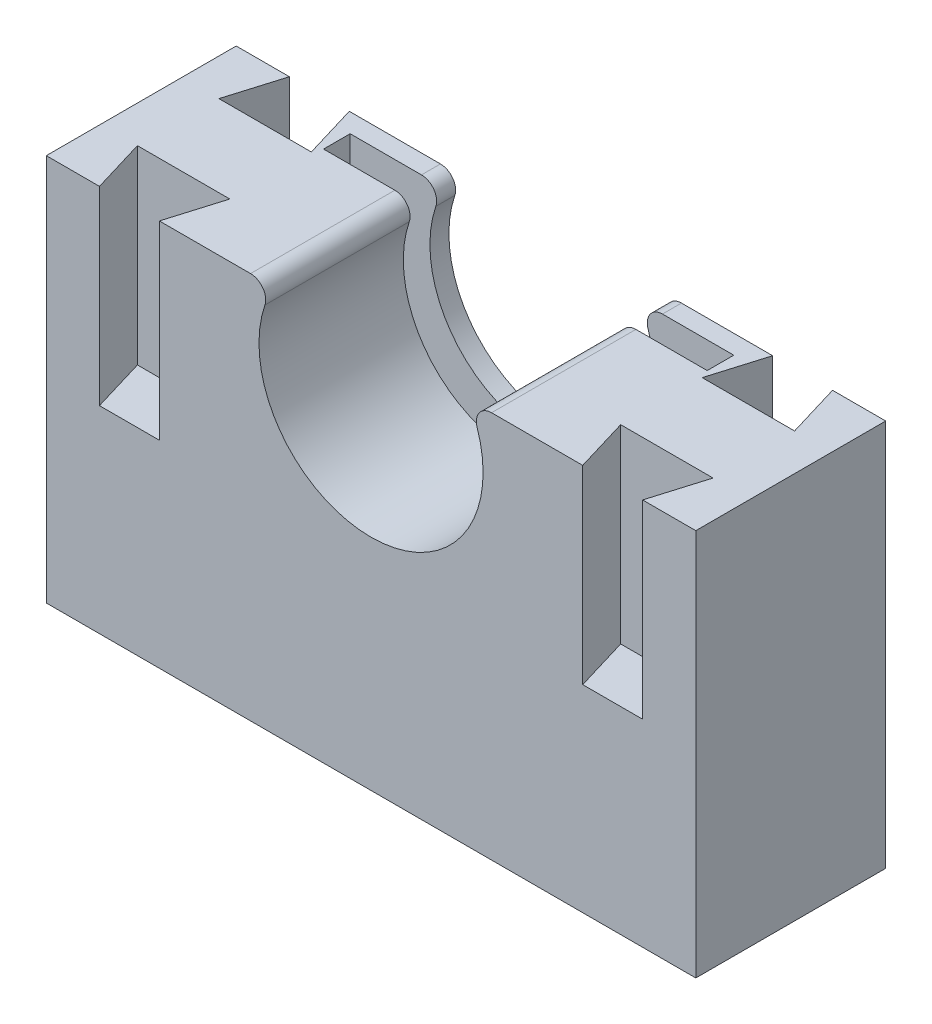
SolidWorks part; units mm, degrees
ref_plane "Front Plane" through (0, 0, 0) normal (0, 0, 1) x (1, 0, 0)
ref_plane "Top Plane" through (0, 0, 0) normal (0, 1, 0) x (1, 0, 0)
ref_plane "Right Plane" through (0, 0, 0) normal (1, 0, 0) x (0, 0, -1)
sketch "Sketch2" plane through (0, 0, 0) normal (0, 0, 1) x (1, 0, 0)
  line L0 (11.1505, 5.8899) -> (11.1505, -22.9851) construction
  line L1 (53.9005, 28.0149) -> (27.0147, 28.0149)
  line L2 (53.9005, 28.0149) -> (53.9005, -22.9851)
  line L3 (53.9005, -22.9851) -> (-31.5995, -22.9851)
  line L4 (-31.5995, 28.0149) -> (-31.5995, -22.9851)
  line L5 (-31.5995, 2.5149) -> (53.9005, 2.5149) construction
  line L6 (-4.7137, 28.0149) -> (-31.5995, 28.0149)
  line L7 (11.1505, 20.6399) -> (11.1505, -22.9851) construction
  line L8 (11.1505, 20.6399) -> (25.1204, 25.3731) construction
  line L9 (-3.5995, 20.6399) -> (25.9005, 20.6399) construction
  arc A0 (-2.8194, 25.3731) -> (25.1204, 25.3731) centre (11.1505, 20.6399) ccw
  arc A1 (-4.7137, 28.0149) -> (-2.8194, 25.3731) centre (-4.7137, 26.0149) cw
  arc A2 (27.0147, 28.0149) -> (25.1204, 25.3731) centre (27.0147, 26.0149) ccw
  dimension "D4" = 2
  dimension "D5" = 29.5
  dimension "D3" = 2
  dimension "D1" = 85.5
  dimension "D2" = 51
extrude "Boss-Extrude1" add sketch "Sketch2" along normal blind 25
sketch "Sketch5" plane through (0, 0, 25) normal (0, 0, 1) x (1, 0, 0)
  line L0 (11.1505, 5.8899) -> (11.1505, 1.4899) construction
  line L1 (-31.5995, -22.9851) -> (53.9005, -22.9851) construction
  line L2 (11.1505, 5.8899) -> (11.1505, 1.4899)
  line L3 (11.1505, -7.3101) -> (11.1505, -22.9851) construction
  arc A0 (-2.8194, 25.3731) -> (25.1204, 25.3731) centre (11.1505, 20.6399) ccw construction
  circle A1 centre (11.1505, -2.9101) radius 4.4
  dimension "D2" = 8.8
  dimension "D1" = 8.8
extrude "Cut-Extrude3" cut sketch "Sketch5" along normal blind 4.5 from surface at -25 contours A1 starting at face at (11.1505, 12.2907, 0)
sketch "Sketch6" plane through (0, 28.0149, 0) normal (0, 1, 0) x (1, 0, 0)
  line L0 (-24.5995, 0) -> (-26.7385, -7.1363)
  line L1 (-4.7137, 0) -> (-31.5995, 0) construction
  line L2 (-26.7385, -7.1363) -> (-14.5747, -7.1363)
  line L3 (-14.5747, -7.1363) -> (-16.7137, 0)
  line L4 (-31.5995, 0) -> (-24.5995, 0)
  line L5 (-16.7137, 0) -> (-4.7137, 0)
  line L6 (-31.5995, -25) -> (-24.5995, -25)
  line L7 (-4.7137, -25) -> (-31.5995, -25) construction
  line L8 (-24.5995, -25) -> (-26.7391, -17.8638)
  line L9 (-26.7391, -17.8638) -> (-14.5741, -17.8638)
  line L10 (-14.5741, -17.8638) -> (-16.7137, -25)
  line L11 (-16.7137, -25) -> (-4.7137, -25)
  line L12 (53.9005, 0) -> (46.9005, 0)
  line L13 (46.9005, 0) -> (49.0401, -7.1362)
  line L14 (49.0401, -7.1362) -> (36.8751, -7.1362)
  line L15 (36.8751, -7.1362) -> (39.0147, 0)
  line L16 (53.9005, 0) -> (27.0147, 0) construction
  line L17 (39.0147, 0) -> (27.0147, 0)
  line L18 (27.0147, -25) -> (39.0147, -25)
  line L19 (53.9005, -25) -> (27.0147, -25) construction
  line L20 (39.0147, -25) -> (36.8751, -17.8638)
  line L21 (36.8751, -17.8638) -> (49.0401, -17.8638)
  line L22 (49.0401, -17.8638) -> (46.9005, -25)
  line L23 (46.9005, -25) -> (53.9005, -25)
  line L24 (-31.5995, 0) -> (-31.5995, -25)
  line L27 (53.9005, 0) -> (53.9005, -25)
  line L28 (-4.7137, 0) -> (27.0147, 0)
  line L29 (27.0147, -25) -> (-4.7137, -25)
  dimension "D1" = 7
  dimension "D2" = 12
  dimension "D3" = 7.45
  dimension "D4" = 7.45
  dimension "D5" = 106.685
  dimension "D6" = 12.1639
  dimension "D7" = 7
  dimension "D8" = 12
  dimension "D9" = 7.45
  dimension "D10" = 7.45
  dimension "D11" = 106.69
  dimension "D12" = 12
  dimension "D13" = 7
  dimension "D14" = 7.45
  dimension "D15" = 7.45
  dimension "D16" = 106.69
  dimension "D17" = 12.165
  dimension "D18" = 12.165
  dimension "D19" = 12
  dimension "D20" = 7
  dimension "D21" = 7.45
  dimension "D22" = 106.69
  dimension "D23" = 7.45
extrude "Cut-Extrude4" cut sketch "Sketch6" against normal blind 25 flip side to cut
ref_plane "Plane1" through (0, 0, 2.5) normal (0, 0, -1) x (-1, 0, 0)
sketch "Sketch8" plane through (0, 0, 2.5) normal (0, 0, -1) x (-1, 0, 0)
  line L0 (-27.0147, 28.0149) -> (4.7137, 28.0149) construction
  line L1 (-11.1505, 28.0149) -> (-11.1505, -7.3101) construction
  line L2 (-36.4005, 2.9448) -> (14.0995, 2.9448)
  line L3 (-36.4005, 2.9448) -> (-36.4005, 28.0149)
  line L4 (-39.0147, 28.0149) -> (-27.0147, 28.0149) construction
  line L5 (-36.4005, 28.0149) -> (14.0995, 28.0149)
  line L6 (4.7137, 28.0149) -> (16.7137, 28.0149) construction
  line L7 (14.0995, 28.0149) -> (14.0995, 2.9448)
  circle A0 centre (-11.1505, -2.9101) radius 4.4 construction
  point P11 (-11.1505, 2.9448)
extrude "Cut-Extrude5" cut sketch "Sketch8" against normal blind 3.5
